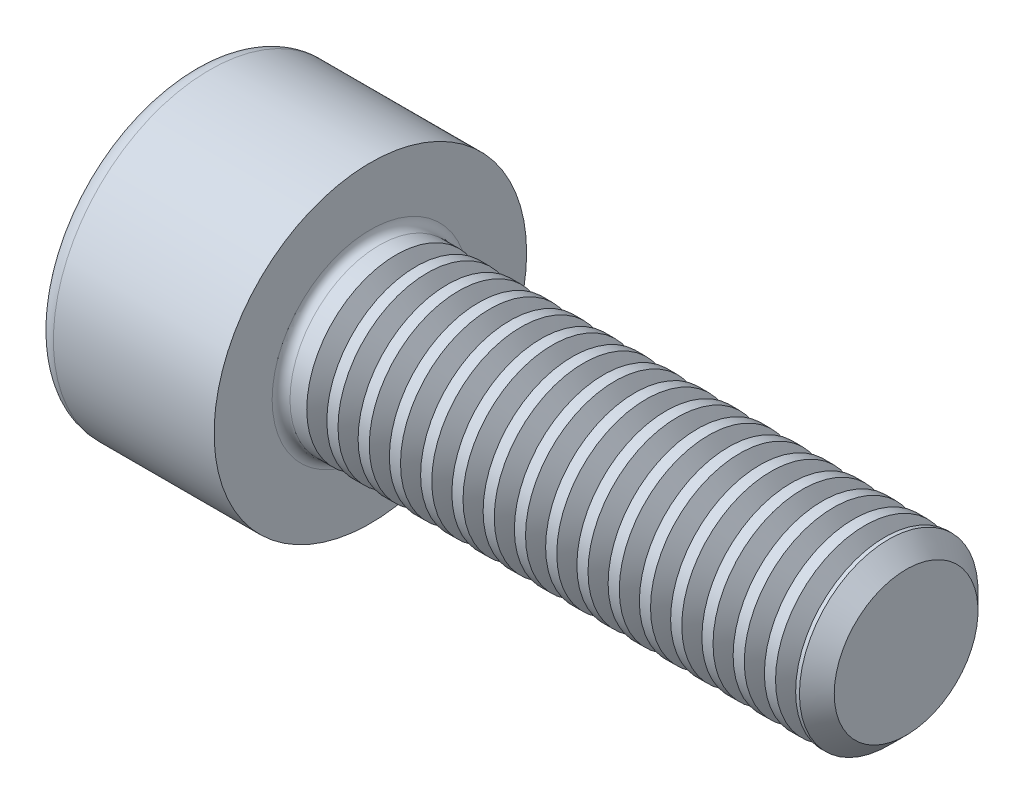
SolidWorks part; units mm, degrees
ref_plane "Front Plane" through (0, 0, 0) normal (0, 0, 1) x (1, 0, 0)
ref_plane "Top Plane" through (0, 0, 0) normal (0, 1, 0) x (1, 0, 0)
ref_plane "Right Plane" through (0, 0, 0) normal (1, 0, 0) x (0, 0, -1)
other "Configuration Table"
sketch "BaseHeadSke" plane through (0, 0, 0) normal (1, 0, 0) x (0, 0, -1)
  circle A1 centre (0, 0) radius 3.5
  dimension "Head_diameter" = 7
extrude "BaseHead" add sketch "BaseHeadSke" along normal blind 4
sketch "BodySke" plane through (0, 0, 0) normal (0, 0, 1) x (1, 0, 0)
  line L0 (0, 0) -> (16, 0)
  line L1 (16, 0) -> (16, 1.61)
  line L2 (16, 1.61) -> (15.61, 2)
  line L3 (15.61, 2) -> (0, 2)
  line L4 (0, 2) -> (0, 0)
  line L6 (0, 0) -> (159.3976, 0) construction
  line L7 (4, -84.3176) -> (4, 77.7215) construction
  line L8 (15.3, -21.5941) -> (15.3, 39.2994) construction
  line L10 (4, -3.5) -> (4, 3.5) construction
  dimension "Ang" = 45
  dimension "Diameter" = 4
  dimension "Minor_dia" = 3.22
  dimension "Thread_length" = 12
  dimension "Advance" = 0.7
  dimension "Length" = 12
revolve "BaseBody" add sketch "BodySke" angle 360 about L6
cosmetic thread "ThreadCosmetic" [suppressed] parameters "Thread_length"=12, "Thread_minor"=3.22
sketch "CutSocketSke" plane through (0, 0, 0) normal (1, 0, 0) x (0, 0, -1)
  line L1 (0, 1.7321) -> (-1.5, 0.866)
  line L2 (-1.5, 0.866) -> (-1.5, -0.866)
  line L3 (-1.5, -0.866) -> (0, -1.7321)
  line L4 (0, -1.7321) -> (1.5, -0.866)
  line L5 (1.5, -0.866) -> (1.5, 0.866)
  line L6 (1.5, 0.866) -> (0, 1.7321)
  circle A0 centre (0, 0) radius 1.5 construction
  dimension "Socket_width" = 3
extrude "CutSocket" cut sketch "CutSocketSke" along normal blind 2
sketch "CutHoleSke" plane through (0, 0, 0) normal (0, 0, 1) x (1, 0, 0)
  line L0 (0, 0) -> (149.4323, 0) construction
  line L1 (0, 1.5) -> (2.6, 1.5)
  line L2 (2.6, 1.5) -> (3.466, 0)
  line L3 (3.466, 0) -> (0, 0)
  line L4 (0, 0) -> (0, 1.5)
  line L6 (4, -3.5) -> (4, 3.5) construction
  dimension "D1" = 60
  dimension "Hole_depth" = 1.4
  dimension "D2" = 3
revolve "CutHole" cut sketch "CutHoleSke" angle 360 about L0
fillet "Fillet1" radius 0.2 1 edges at (4, 0, -2)
fillet "Fillet2" radius 0.4 1 edges at (0, 0, -3.5)
sketch "ThdSchSke" plane through (0, 0, 0) normal (0, 0, 1) x (1, 0, 0)
  line L0 (15.0748, 2.4503) -> (15.0748, 2)
  line L1 (15.0748, 2) -> (15.3, 1.61)
  line L2 (15.3, 1.61) -> (15.5252, 2)
  line L3 (15.5252, 2) -> (15.5252, 2.4503)
  line L4 (15.5252, 2.4503) -> (15.0748, 2.4503)
  line L6 (0, 0) -> (141.9934, 0) construction
  line L7 (16, -1.61) -> (16, 1.61) construction
  dimension "Advance" = 0.7
  dimension "D2" = 3.22
  dimension "D3" = 4
revolve "ThreadSchematic" cut sketch "ThdSchSke" angle 360 about L6
pattern_linear "ThdSchPat" count 16 spacing 0.7 along (-1, 0, 0) of "ThreadSchematic"
equation "\"Thread_minor@ThreadCosmetic\" = \"Minor_dia@BodySke\""
equation "\"Thread_length@ThreadCosmetic\" = \"Thread_length@BodySke\""
equation "\"D2@CutHoleSke\" = \"Socket_width@CutSocketSke\""
equation "\"D2@ThdSchSke\" = \"Minor_dia@BodySke\""
equation "\"D3@ThdSchSke\" = \"Diameter@BodySke\""
equation "\"Advance@ThdSchSke\" = \"Advance@BodySke\""
equation "\"D3@ThdSchPat\" = \"Advance@BodySke\""
equation "\"D1@ThdSchPat\" =  int( \"Thread_length@BodySke\"/\"Advance@BodySke\" )-1"
